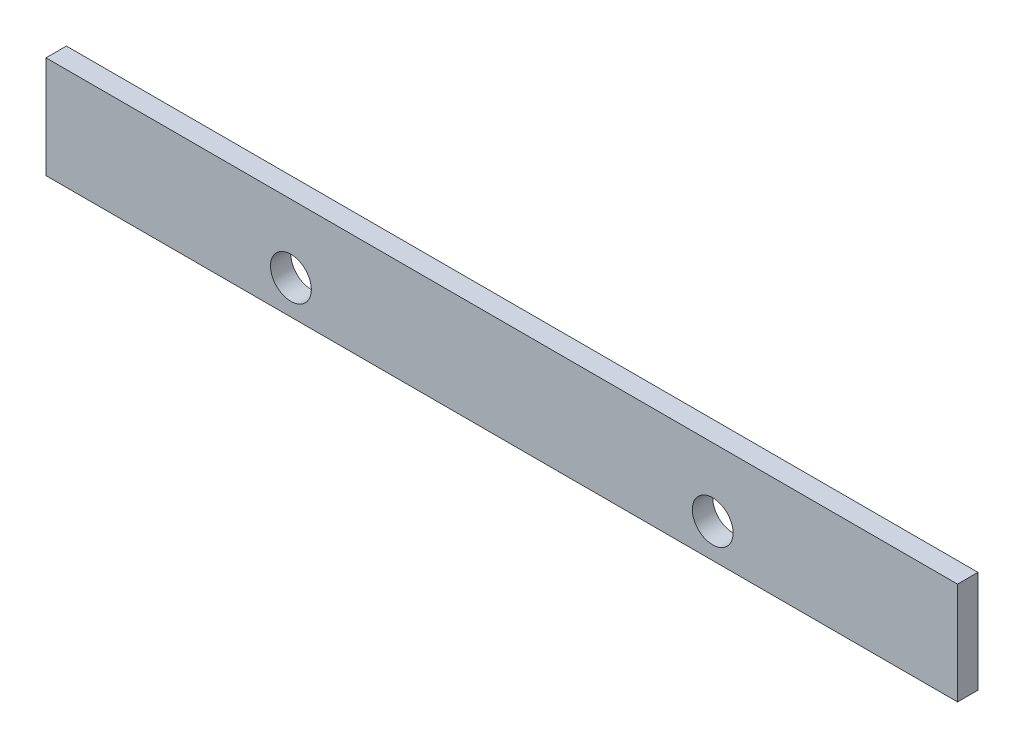
SolidWorks part; units mm, degrees
ref_plane "Front Plane" through (0, 0, 0) normal (0, 0, 1) x (1, 0, 0)
ref_plane "Top Plane" through (0, 0, 0) normal (0, 1, 0) x (1, 0, 0)
ref_plane "Right Plane" through (0, 0, 0) normal (1, 0, 0) x (0, 0, -1)
sketch "Sketch1" plane through (0, 0, 0) normal (0, 0, 1) x (1, 0, 0)
  line L1 (-67, 7.5) -> (67, 7.5)
  line L2 (-67, 7.5) -> (-67, -7.5)
  line L3 (-67, -7.5) -> (67, -7.5)
  line L4 (67, 7.5) -> (67, -7.5)
  line L5 (-67, 7.5) -> (67, -7.5) construction
  line L6 (-67, -7.5) -> (67, 7.5) construction
  point P0 (0, 0)
extrude "Boss-Extrude1" add sketch "Sketch1" along normal blind 3
sketch "Sketch2" plane through (0, 0, 0) normal (0, 0, -1) x (-1, 0, 0)
  line L0 (67, -7.5) -> (31, -7.5)
  line L1 (67, -7.5) -> (-67, -7.5) construction
  line L2 (31, -7.5) -> (31, -2.5)
  circle A0 centre (31, -2.5) radius 3
sketch "Sketch3" plane through (0, 0, 0) normal (0, 0, -1) x (-1, 0, 0)
  line L0 (-67, -7.5) -> (-31, -7.5)
  line L1 (67, -7.5) -> (-67, -7.5) construction
  line L2 (-31, -7.5) -> (-31, -2.5)
sketch "Sketch4" plane through (0, 0, 0) normal (0, 0, -1) x (-1, 0, 0)
  circle A0 centre (-31, -2.5) radius 3
extrude "Cut-Extrude1" cut sketch "Sketch4" against normal blind 3
extrude "Cut-Extrude2" cut sketch "Sketch2" against normal blind 3 contours A0
